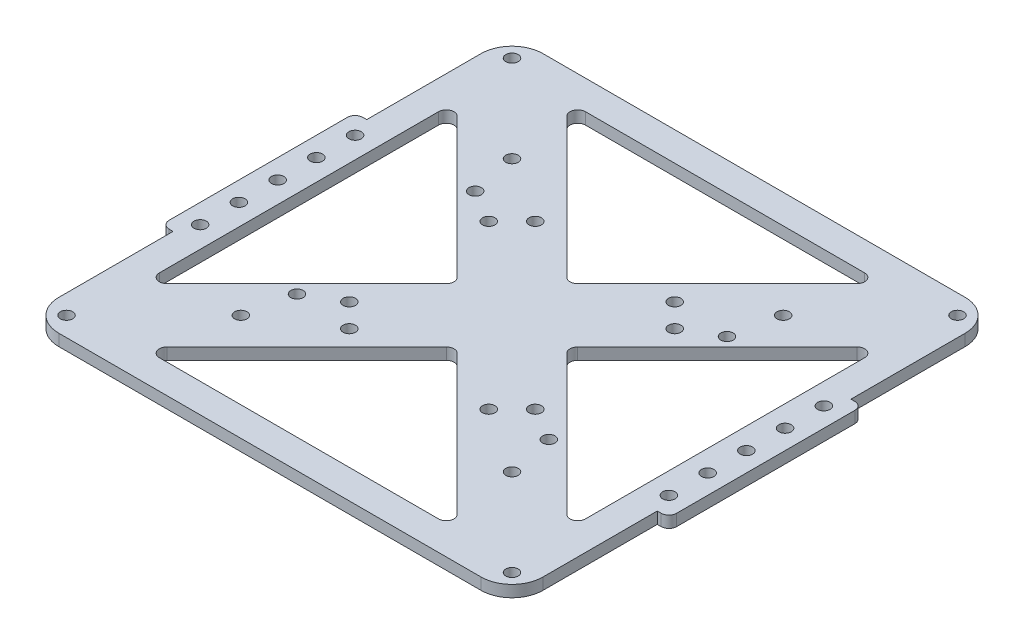
SolidWorks part; units mm, degrees
ref_plane "前视基准面" through (0, 0, 0) normal (0, 0, 1) x (1, 0, 0)
ref_plane "上视基准面" through (0, 0, 0) normal (0, 1, 0) x (1, 0, 0)
ref_plane "右视基准面" through (0, 0, 0) normal (1, 0, 0) x (0, 0, -1)
sketch "草图1" plane through (0, 0, 0) normal (0, 1, 0) x (1, 0, 0)
  line L1 (-57.5, 57.5) -> (57.5, 57.5) construction
  line L2 (-57.5, 57.5) -> (-57.5, -57.5) construction
  line L3 (-57.5, -57.5) -> (57.5, -57.5) construction
  line L4 (57.5, 57.5) -> (57.5, -57.5) construction
  line L5 (-57.5, 57.5) -> (57.5, -57.5) construction
  line L6 (-57.5, -57.5) -> (0, 0) construction
  line L7 (-54.5, -62.5) -> (54.5, -62.5)
  line L8 (-62.5, -54.5) -> (-62.5, 54.5)
  line L9 (-54.5, 62.5) -> (54.5, 62.5)
  line L10 (62.5, -54.5) -> (62.5, 54.5)
  line L11 (-62.5, -62.5) -> (62.5, 62.5) construction
  line L12 (-62.5, 62.5) -> (62.5, -62.5) construction
  line L13 (-35, -35) -> (35, -35) construction
  line L14 (-35, -35) -> (-35, 35) construction
  line L15 (-35, 35) -> (35, 35) construction
  line L16 (35, -35) -> (35, 35) construction
  line L17 (-35, -35) -> (35, 35) construction
  line L18 (-35, 35) -> (35, -35) construction
  line L19 (-32.5, -23) -> (32.5, -23) construction
  line L20 (-32.5, -23) -> (-32.5, 23) construction
  line L21 (-32.5, 23) -> (32.5, 23) construction
  line L22 (32.5, -23) -> (32.5, 23) construction
  line L23 (-32.5, -23) -> (32.5, 23) construction
  line L24 (-32.5, 23) -> (32.5, -23) construction
  line L29 (-52.5, -52.5) -> (52.5, 52.5) construction
  line L30 (-52.5, 52.5) -> (52.5, -52.5) construction
  line L36 (6, 6) -> (57.5, 57.5) construction
  line L39 (-40, 30) -> (-30, 30) construction
  line L40 (-40, 30) -> (-40, 40) construction
  line L42 (-40, 40) -> (-30, 40) construction
  line L43 (-32.5, 0) -> (-62.5, 0) construction
  line L44 (-60.5, -60.5) -> (60.5, -60.5) construction
  line L45 (-60.5, -60.5) -> (-60.5, 60.5) construction
  line L46 (-60.5, 60.5) -> (60.5, 60.5) construction
  line L47 (60.5, -60.5) -> (60.5, 60.5) construction
  line L48 (-60.5, -60.5) -> (60.5, 60.5) construction
  line L49 (-60.5, 60.5) -> (60.5, -60.5) construction
  line L50 (0, 0) -> (0, 62.5) construction
  line L51 (55.5, 25) -> (63.5, 25)
  line L52 (-55.5, -25) -> (-63.5, -25)
  line L53 (-55.5, -25) -> (-55.5, 25)
  line L54 (-55.5, 25) -> (-63.5, 25)
  line L55 (-65.5, -23) -> (-65.5, 23)
  line L56 (-55.5, -25) -> (-65.5, 25) construction
  line L57 (-55.5, 25) -> (-65.5, -25) construction
  line L58 (65.5, -23) -> (65.5, 23)
  line L59 (55.5, -25) -> (63.5, -25)
  line L60 (55.5, -25) -> (55.5, 25)
  line L61 (-30, 30) -> (-30, 40) construction
  line L62 (-24, -18) -> (24, -18) construction
  line L63 (-24, -18) -> (-24, 18) construction
  line L64 (-24, 18) -> (24, 18) construction
  line L65 (24, -18) -> (24, 18) construction
  line L66 (-24, -18) -> (24, 18) construction
  line L67 (-24, 18) -> (24, -18) construction
  line L68 (-55, -55) -> (55, -55) construction
  line L69 (-55, -55) -> (-55, 55) construction
  line L70 (-55, 55) -> (55, 55) construction
  line L71 (55, -55) -> (55, 55) construction
  line L72 (-55, -55) -> (55, 55) construction
  line L73 (-55, 55) -> (55, -55) construction
  line L74 (-40, 30) -> (-30, 40) construction
  line L75 (-40, 40) -> (-30, 30) construction
  line L76 (-37.5, 18) -> (-27.5, 18) construction
  line L77 (-37.5, 18) -> (-37.5, 28) construction
  line L78 (-37.5, 28) -> (-27.5, 28) construction
  line L79 (-27.5, 18) -> (-27.5, 28) construction
  line L80 (-37.5, 18) -> (-27.5, 28) construction
  line L81 (-37.5, 28) -> (-27.5, 18) construction
  line L82 (-29, 13) -> (-19, 13) construction
  line L83 (-29, 13) -> (-29, 23) construction
  line L84 (-29, 23) -> (-19, 23) construction
  line L85 (-19, 13) -> (-19, 23) construction
  line L86 (-29, 13) -> (-19, 23) construction
  line L87 (-29, 23) -> (-19, 13) construction
  line L88 (-5, -5) -> (5, -5) construction
  line L89 (-5, -5) -> (-5, 5) construction
  line L90 (-5, 5) -> (5, 5) construction
  line L91 (5, -5) -> (5, 5) construction
  line L92 (-5, -5) -> (5, 5) construction
  line L93 (-5, 5) -> (5, -5) construction
  line L98 (-55, 55) -> (55, -55) construction
  line L99 (-55, -55) -> (55, 55) construction
  circle A0 centre (-57.5, 57.5) radius 1.6
  circle A1 centre (57.5, 57.5) radius 1.6
  circle A2 centre (57.5, -57.5) radius 1.6
  circle A3 centre (-57.5, -57.5) radius 1.6
  arc A4 (62.5, -54.5) -> (54.5, -62.5) centre (54.5, -54.5) cw
  arc A5 (-62.5, -54.5) -> (-54.5, -62.5) centre (-54.5, -54.5) ccw
  arc A6 (-62.5, 54.5) -> (-54.5, 62.5) centre (-54.5, 54.5) cw
  arc A7 (54.5, 62.5) -> (62.5, 54.5) centre (54.5, 54.5) cw
  circle A8 centre (-35, 35) radius 1.6
  circle A9 centre (35, 35) radius 1.6
  circle A10 centre (-35, -35) radius 1.6
  circle A11 centre (35, -35) radius 1.6
  circle A12 centre (-32.5, 23) radius 1.6
  circle A13 centre (32.5, 23) radius 1.6
  circle A14 centre (-32.5, -23) radius 1.6
  circle A15 centre (32.5, -23) radius 1.6
  circle A32 centre (-60.5, 0) radius 1.6
  circle A33 centre (-60.5, 10) radius 1.6
  circle A34 centre (-60.5, 20) radius 1.6
  circle A35 centre (-60.5, -20) radius 1.6
  circle A36 centre (-60.5, -10) radius 1.6
  circle A37 centre (60.5, -10) radius 1.6
  circle A38 centre (60.5, -20) radius 1.6
  circle A39 centre (60.5, 20) radius 1.6
  circle A40 centre (60.5, 10) radius 1.6
  circle A41 centre (60.5, 0) radius 1.6
  arc A42 (-63.5, -25) -> (-65.5, -23) centre (-63.5, -23) cw
  arc A43 (-65.5, 23) -> (-63.5, 25) centre (-63.5, 23) cw
  arc A44 (65.5, 23) -> (63.5, 25) centre (63.5, 23) ccw
  arc A45 (63.5, -25) -> (65.5, -23) centre (63.5, -23) ccw
  circle A46 centre (-24, 18) radius 1.6
  circle A47 centre (24, 18) radius 1.6
  circle A48 centre (24, -18) radius 1.6
  circle A49 centre (-24, -18) radius 1.6
  circle A50 centre (18, 24) radius 1.6
  circle A51 centre (18, -24) radius 1.6
  circle A52 centre (-18, -24) radius 1.6
  circle A53 centre (-18, 24) radius 1.6
  circle A54 centre (24, -18) radius 1.6
  circle A55 centre (-24, -18) radius 1.6
  circle A56 centre (-24, 18) radius 1.6
  circle A57 centre (24, 18) radius 1.6
  circle A58 centre (-18, -24) radius 1.6
  circle A59 centre (-18, 24) radius 1.6
  circle A60 centre (18, 24) radius 1.6
  circle A61 centre (18, -24) radius 1.6
  point P0 (0, 0)
  point P10 (0, 0)
  point P27 (0, 0)
  point P36 (0, 0)
  point P45 (0, 0)
  point P101 (0, -12)
  point P108 (0, 0)
  dimension "D1" = 8
  dimension "D2" = 110
  dimension "D3" = 110
  dimension "D4" = 4
  dimension "D5" = 2
extrude "凸台-拉伸2" add sketch "草图1" along normal blind 3
sketch "草图2" plane through (0, 0, 0) normal (0, 1, 0) x (1, 0, 0)
  line L0 (-51.5858, 37.4437) -> (-15.5563, 1.4142)
  line L1 (-36.0294, 55) -> (36.0294, 55)
  line L2 (-55, 36.0294) -> (-55, -36.0294)
  line L3 (-36.0294, -55) -> (36.0294, -55)
  line L4 (55, 36.0294) -> (55, -36.0294)
  line L5 (-55, 55) -> (55, -55) construction
  line L6 (-55, -55) -> (55, 55) construction
  line L7 (37.4437, 51.5858) -> (1.4142, 15.5563)
  line L8 (51.5858, -37.4437) -> (15.5563, -1.4142)
  line L9 (-37.4437, -51.5858) -> (-1.4142, -15.5563)
  line L10 (-15.5563, -1.4142) -> (-51.5858, -37.4437)
  line L11 (1.4142, -15.5563) -> (37.4437, -51.5858)
  line L12 (15.5563, 1.4142) -> (51.5858, 37.4437)
  line L13 (-1.4142, 15.5563) -> (-37.4437, 51.5858)
  arc A0 (-36.0294, 55) -> (-37.4437, 51.5858) centre (-36.0294, 53) ccw
  arc A1 (37.4437, 51.5858) -> (36.0294, 55) centre (36.0294, 53) ccw
  arc A2 (55, 36.0294) -> (51.5858, 37.4437) centre (53, 36.0294) ccw
  arc A3 (51.5858, -37.4437) -> (55, -36.0294) centre (53, -36.0294) ccw
  arc A4 (36.0294, -55) -> (37.4437, -51.5858) centre (36.0294, -53) ccw
  arc A5 (-37.4437, -51.5858) -> (-36.0294, -55) centre (-36.0294, -53) ccw
  arc A6 (-55, -36.0294) -> (-51.5858, -37.4437) centre (-53, -36.0294) ccw
  arc A7 (-51.5858, 37.4437) -> (-55, 36.0294) centre (-53, 36.0294) ccw
  arc A8 (1.4142, -15.5563) -> (-1.4142, -15.5563) centre (0, -16.9706) ccw
  arc A9 (15.5563, 1.4142) -> (15.5563, -1.4142) centre (16.9706, 0) ccw
  arc A10 (1.4142, 15.5563) -> (-1.4142, 15.5563) centre (0, 16.9706) cw
  arc A11 (-15.5563, -1.4142) -> (-15.5563, 1.4142) centre (-16.9706, 0) ccw
  point P0 (0, 0)
  point P17 (0, 0)
  point P41 (0, 14.1421)
  dimension "D5" = 2
  dimension "D6" = 2
  dimension "D1" = 110
  dimension "D2" = 110
  dimension "D3" = 20
  dimension "D4" = 4
extrude "切除-拉伸2" cut sketch "草图2" along normal through all
